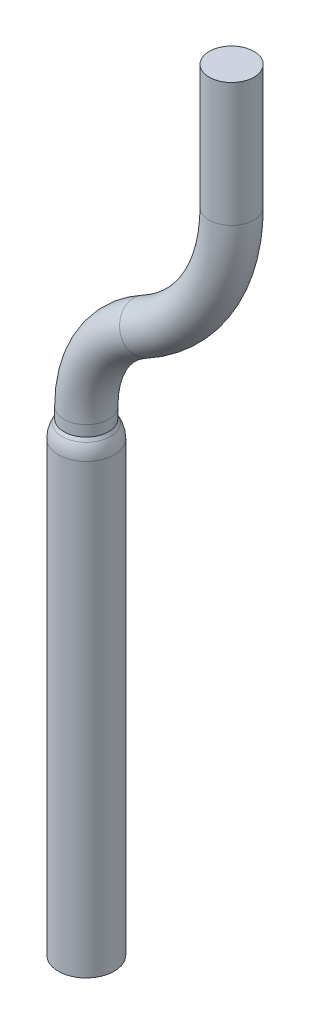
SolidWorks part; units mm, degrees
material "Copper"
ref_plane "Front Plane" through (0, 0, 0) normal (0, 0, 1) x (1, 0, 0)
ref_plane "Top Plane" through (0, 0, 0) normal (0, 1, 0) x (1, 0, 0)
ref_plane "Right Plane" through (0, 0, 0) normal (1, 0, 0) x (0, 0, -1)
sketch "Sketch1" plane through (0, 0, 0) normal (0, 0, 1) x (1, 0, 0)
  line L0 (-7.5, 30.2) -> (-7.5, 25.7727)
  line L2 (-12.7, 17) -> (-12.7, 0)
  line L3 (55, 0) -> (-55, 0) construction
  line L4 (0, -55) -> (0, 55) construction
  arc A0 (-12.7, 17) -> (-10.62, 20.5091) centre (-8.7, 17) cw
  arc A1 (-7.5, 25.7727) -> (-10.62, 20.5091) centre (-13.5, 25.7727) cw
  dimension "D1" = 4
  dimension "D6" = 6
  dimension "D2" = 12.7
  dimension "D3" = 5.2
  dimension "D4" = 17
  dimension "D5" = 30.2
sketch "Sketch2" plane through (0, 0, 0) normal (0, 1, 0) x (1, 0, 0)
  line L0 (-12.7, 0) -> (-10.62, 0) construction
  line L1 (-55, 0) -> (55, 0) construction
  circle A0 centre (-12.7, 0) radius 0.8
  dimension "D1" = 1.6
sweep "Sweep1" add profiles "Sketch2" path "Sketch1"
sketch "Sketch3" plane through (0, 0, 0) normal (0, 0, 1) x (1, 0, 0)
  line L0 (-12.7, 21.8194) -> (-12.7, -3.5848) construction
  line L1 (0, -0.88) -> (0, 0.88) construction
  line L2 (-12.7, 0) -> (-11.7, 0)
  line L3 (0.88, 0) -> (-0.88, 0) construction
  line L4 (-11.7, 0) -> (-11.7, 16)
  line L5 (-11.834, 16.5) -> (-12.7, 18)
  line L6 (-12.7, 18) -> (-12.7, 0)
  arc A0 (-11.7, 16) -> (-11.834, 16.5) centre (-12.7, 16) ccw
  dimension "D2" = 1
  dimension "D1" = 12.7
  dimension "D3" = 2
  dimension "D4" = 16
  dimension "D5" = 30
revolve "Revolve1" add sketch "Sketch3" angle 360 about L0
